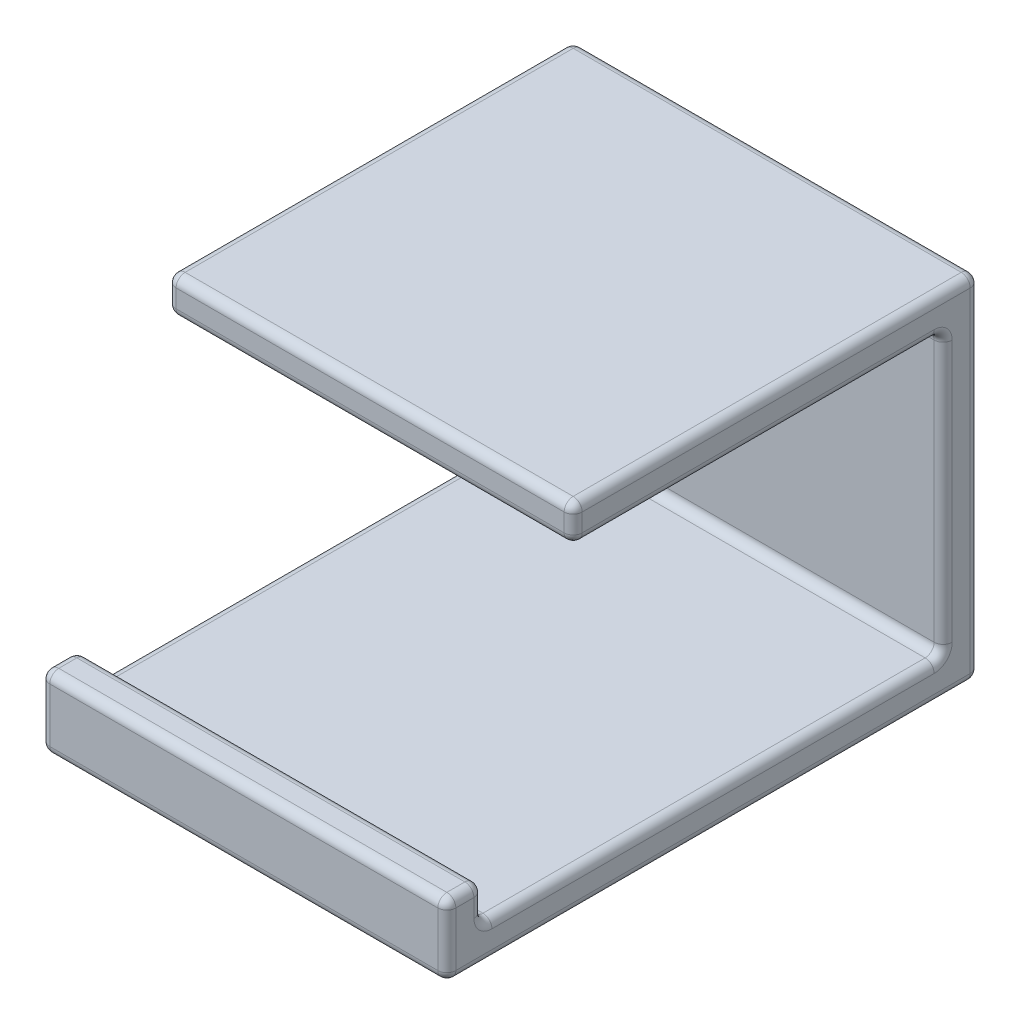
SolidWorks part; units mm, degrees
ref_plane "Plano frontal" through (0, 0, 0) normal (0, 0, 1) x (1, 0, 0)
ref_plane "Plano superior" through (0, 0, 0) normal (0, 1, 0) x (1, 0, 0)
ref_plane "Plano direito" through (0, 0, 0) normal (1, 0, 0) x (0, 0, -1)
sketch "Esboço1" plane through (0, 0, 0) normal (0, 0, 1) x (1, 0, 0)
  line L1 (-20.3172, 16.5339) -> (24.6828, 16.5339)
  line L2 (-20.3172, 16.5339) -> (-20.3172, -18.4661)
  line L3 (-20.3172, -18.4661) -> (24.6828, -18.4661)
  line L4 (24.6828, 16.5339) -> (24.6828, -18.4661)
  dimension "D1" = 45
  dimension "D2" = 35
extrude "Ressalto-extrusão1" add sketch "Esboço1" along normal blind 4
sketch "Esboço2" plane through (0, 16.5339, 0) normal (0, 1, 0) x (1, 0, 0)
  line L1 (-20.3172, 0) -> (24.6828, 0)
  line L2 (-20.3172, 0) -> (-20.3172, -45)
  line L3 (-20.3172, -45) -> (24.6828, -45)
  line L4 (24.6828, 0) -> (24.6828, -45)
  dimension "D1" = 45
  dimension "D2" = 45
extrude "Ressalto-extrusão2" add sketch "Esboço2" along normal blind 4
sketch "Esboço3" plane through (0, 0, 4) normal (0, 0, 1) x (1, 0, 0)
  line L0 (-20.3172, 16.5339) -> (-20.3172, -18.4661) construction
  line L1 (24.6828, -18.4661) -> (-20.3172, -18.4661)
  line L2 (24.6828, -18.4661) -> (24.6828, -14.4661)
  line L3 (24.6828, -14.4661) -> (-20.3172, -14.4661)
  line L4 (-20.3172, -18.4661) -> (-20.3172, -14.4661)
  dimension "D1" = 4
  dimension "D2" = 45
extrude "Ressalto-extrusão3" add sketch "Esboço3" along normal blind 55
sketch "Esboço4" plane through (0, -14.4661, 0) normal (0, 1, 0) x (1, 0, 0)
  line L0 (24.6828, -59) -> (24.6828, -4) construction
  line L1 (-20.3172, -59) -> (24.6828, -59)
  line L2 (-20.3172, -59) -> (-20.3172, -55)
  line L3 (-20.3172, -55) -> (24.6828, -55)
  line L4 (24.6828, -59) -> (24.6828, -55)
  dimension "D1" = 45
  dimension "D2" = 4
extrude "Ressalto-extrusão4" add sketch "Esboço4" along normal blind 4
fillet "Filete1" radius 1 30 edges at (-20.3172, -18.4661, 29.5) (24.6828, -18.4661, 29.5) (2.1828, 16.5339, 4) (24.6828, 1.0339, 4) (-20.3172, 1.0339, 4) (24.6828, 1.0339, 0) (2.1828, -18.4661, 0) (2.1828, -18.4661, 59) (-20.3172, 1.0339, 0) (-20.3172, 18.5339, 45) (24.6828, 18.5339, 45) (2.1828, 20.5339, 0) (24.6828, 20.5339, 22.5) (2.1828, 20.5339, 45) (-20.3172, 20.5339, 22.5) (24.6828, 16.5339, 24.5) (2.1828, 16.5339, 45) (-20.3172, 16.5339, 24.5) (24.6828, -14.4661, 29.5) (-20.3172, -14.4661, 29.5) (-20.3172, -14.4661, 59) (24.6828, -14.4661, 59) (2.1828, -14.4661, 4) (24.6828, -12.4661, 55) (-20.3172, -12.4661, 55) (2.1828, -10.4661, 55) (24.6828, -10.4661, 57) (2.1828, -10.4661, 59) (-20.3172, -10.4661, 57) (2.1828, -14.4661, 55)
